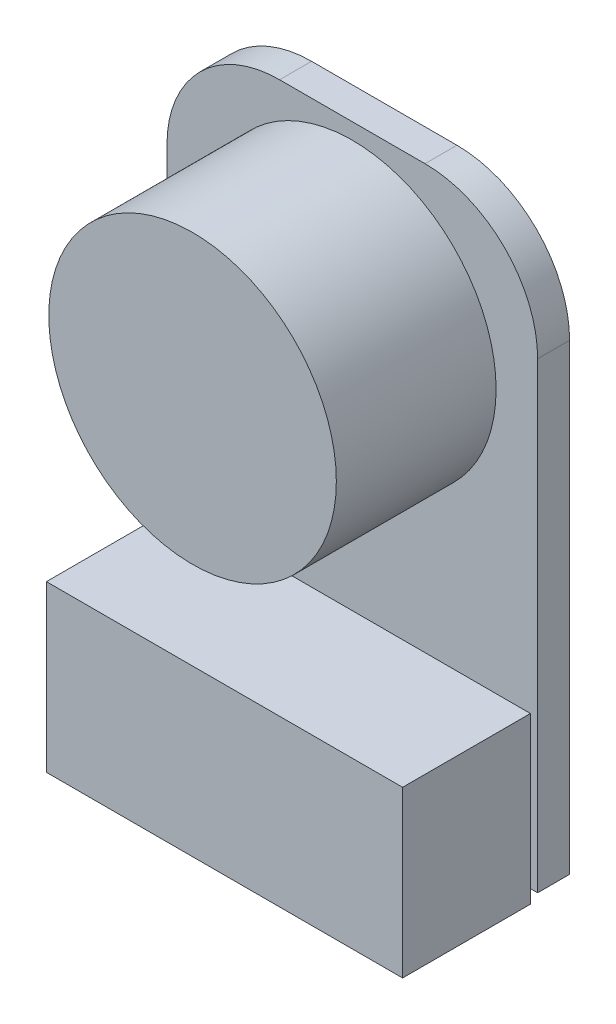
SolidWorks part; units mm, degrees
ref_plane "前视基准面" through (0, 0, 0) normal (0, 0, 1) x (1, 0, 0)
ref_plane "上视基准面" through (0, 0, 0) normal (0, 1, 0) x (1, 0, 0)
ref_plane "右视基准面" through (0, 0, 0) normal (1, 0, 0) x (0, 0, -1)
sketch "草图1" plane through (0, 0, 0) normal (0, 0, 1) x (1, 0, 0)
  line L0 (0, -55) -> (0, 55) construction
  line L1 (-2.275, 5) -> (2.275, 5)
  line L2 (-5.8006, 1.4744) -> (-5.8006, -13)
  line L3 (-5.8006, -13) -> (5.8006, -13)
  line L4 (5.8006, 1.4744) -> (5.8006, -13)
  line L5 (-4.9855, 3.729) -> (5.8006, -13) construction
  line L6 (-5.8006, -13) -> (5.8006, 5) construction
  circle A0 centre (0, 0) radius 4.5 construction
  arc A1 (-5.8006, 1.4744) -> (-2.275, 5) centre (-2.275, 1.4744) cw
  arc A2 (5.8006, 1.4744) -> (2.275, 5) centre (2.275, 1.4744) ccw
  point P3 (-0.0011, -4.0017)
  point P5 (0, 0)
  point P16 (-5.8501, 1.6289)
  point P17 (-3.7802, 5)
  point P18 (-5.8124, 2.1276)
  point P19 (-5.7932, 1.4744)
  dimension "D1" = 9
  dimension "D2" = 5
  dimension "D3" = 18
extrude "凸台-拉伸1" add sketch "草图1" along normal blind 1 contours A0 | L4 L3 L2 A1 L1 A2
sketch "草图2" plane through (0, 0, 1) normal (0, 0, 1) x (1, 0, 0)
  circle A0 centre (0, 0) radius 4.5
extrude "凸台-拉伸2" add sketch "草图2" along normal blind 5
sketch "草图3" plane through (0, 0, 1) normal (0, 0, 1) x (1, 0, 0)
  line L1 (-5.5742, -8.2532) -> (5.5742, -8.2532)
  line L2 (-5.5742, -8.2532) -> (-5.5742, -13.4226)
  line L3 (-5.5742, -13.4226) -> (5.5742, -13.4226)
  line L4 (5.5742, -8.2532) -> (5.5742, -13.4226)
  line L5 (-5.5742, -8.2532) -> (5.5742, -13.4226) construction
  line L6 (-5.5742, -13.4226) -> (5.5742, -8.2532) construction
  point P0 (0, -10.8379)
  point P5 (3.6243, -12.8605)
  point P6 (3.6243, -12.8605)
  point P7 (3.6243, -12.8605)
  dimension "D2" = 0
extrude "凸台-拉伸3" add sketch "草图3" along normal blind 4
